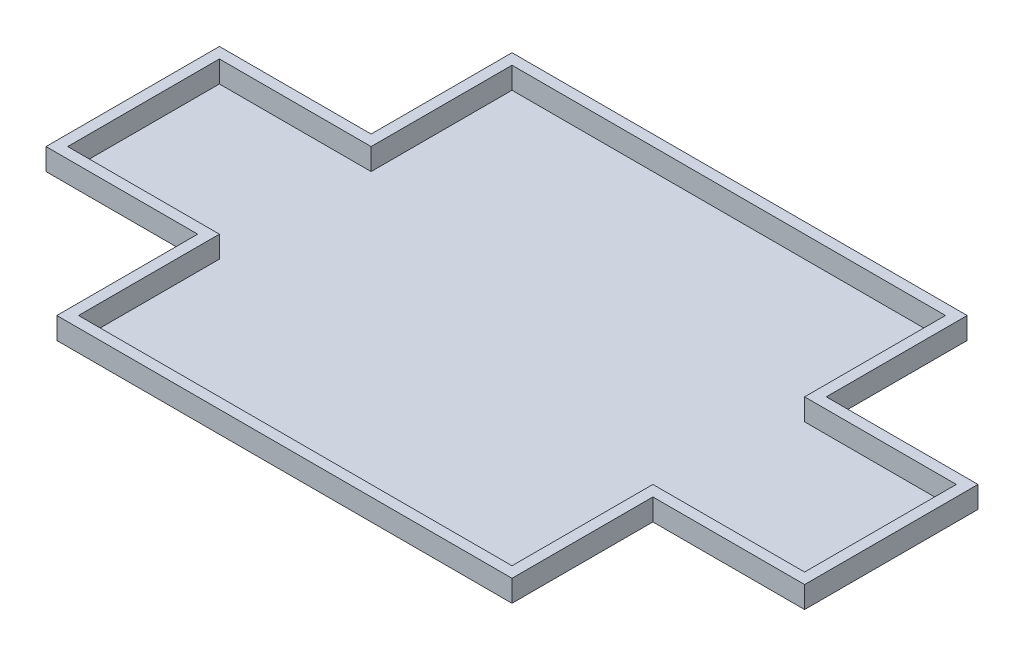
SolidWorks part; units mm, degrees
ref_plane "Alzado" through (0, 0, 0) normal (0, 0, 1) x (1, 0, 0)
ref_plane "Planta" through (0, 0, 0) normal (0, 1, 0) x (1, 0, 0)
ref_plane "Vista lateral" through (0, 0, 0) normal (1, 0, 0) x (0, 0, -1)
sketch "Croquis1" plane through (0, 0, 0) normal (0, 1, 0) x (1, 0, 0)
  line L0 (0, 1350) -> (0, 2000)
  line L1 (0, 0) -> (2000, 0)
  line L2 (0, 0) -> (0, 650)
  line L3 (0, 2000) -> (2000, 2000)
  line L4 (2000, 0) -> (2000, 650)
  line L5 (-700, 1350) -> (0, 1350)
  line L6 (-700, 1350) -> (-700, 650)
  line L7 (-700, 650) -> (0, 650)
  line L9 (2000, 1350) -> (2700, 1350)
  line L11 (2000, 650) -> (2700, 650)
  line L12 (2700, 1350) -> (2700, 650)
  line L13 (2000, 1350) -> (2000, 2000)
  dimension "D1" = 2000
  dimension "D2" = 700
  dimension "D3" = 700
  dimension "D4" = 650
  dimension "D5" = 650
  dimension "D6" = 650
  dimension "D7" = 700
  dimension "D8" = 700
extrude "Saliente-Extruir1" add sketch "Croquis1" along normal blind 20
sketch "Croquis2" plane through (0, 20, 0) normal (0, 1, 0) x (1, 0, 0)
  line L0 (-750, 600) -> (-750, 1400)
  line L1 (-750, 1400) -> (-50, 1400)
  line L2 (-50, 1400) -> (-50, 2050)
  line L3 (-50, 2050) -> (2050, 2050)
  line L4 (2050, 2050) -> (2050, 1400)
  line L5 (2050, 1400) -> (2750, 1400)
  line L6 (2750, 1400) -> (2750, 600)
  line L7 (2750, 600) -> (2050, 600)
  line L8 (2050, 600) -> (2050, -50)
  line L9 (2050, -50) -> (-50, -50)
  line L10 (-50, -50) -> (-50, 600)
  line L11 (-50, 600) -> (-750, 600)
  line L13 (0, 1350) -> (-700, 1350) construction
  line L14 (-700, 1350) -> (-700, 650) construction
  line L16 (2000, 650) -> (2700, 650) construction
  line L17 (2700, 650) -> (2700, 1350) construction
  line L18 (2700, 1350) -> (2000, 1350) construction
  line L19 (-700, 1350) -> (0, 1350)
  line L20 (0, 1350) -> (0, 2000)
  line L21 (0, 2000) -> (2000, 2000)
  line L22 (2000, 2000) -> (2000, 1350)
  line L23 (2000, 1350) -> (2700, 1350)
  line L24 (2700, 1350) -> (2700, 650)
  line L25 (2700, 650) -> (2000, 650)
  line L26 (2000, 650) -> (2000, 0)
  line L27 (2000, 0) -> (0, 0)
  line L28 (0, 0) -> (0, 650)
  line L29 (0, 650) -> (-700, 650)
  line L30 (-700, 650) -> (-700, 1350)
  point P46 (0, 0)
  point P47 (0, 0)
  point P48 (0, 0)
  dimension "D1" = 800
  dimension "D2" = 700
  dimension "D3" = 650
  dimension "D4" = 650
  dimension "D5" = 50
  dimension "D6" = 50
  dimension "D7" = 2100
  dimension "D8" = 2100
  dimension "D9" = 50
  dimension "D10" = 50
  dimension "D11" = 50
extrude "Saliente-Extruir2" add sketch "Croquis2" along normal blind 100 separate body
